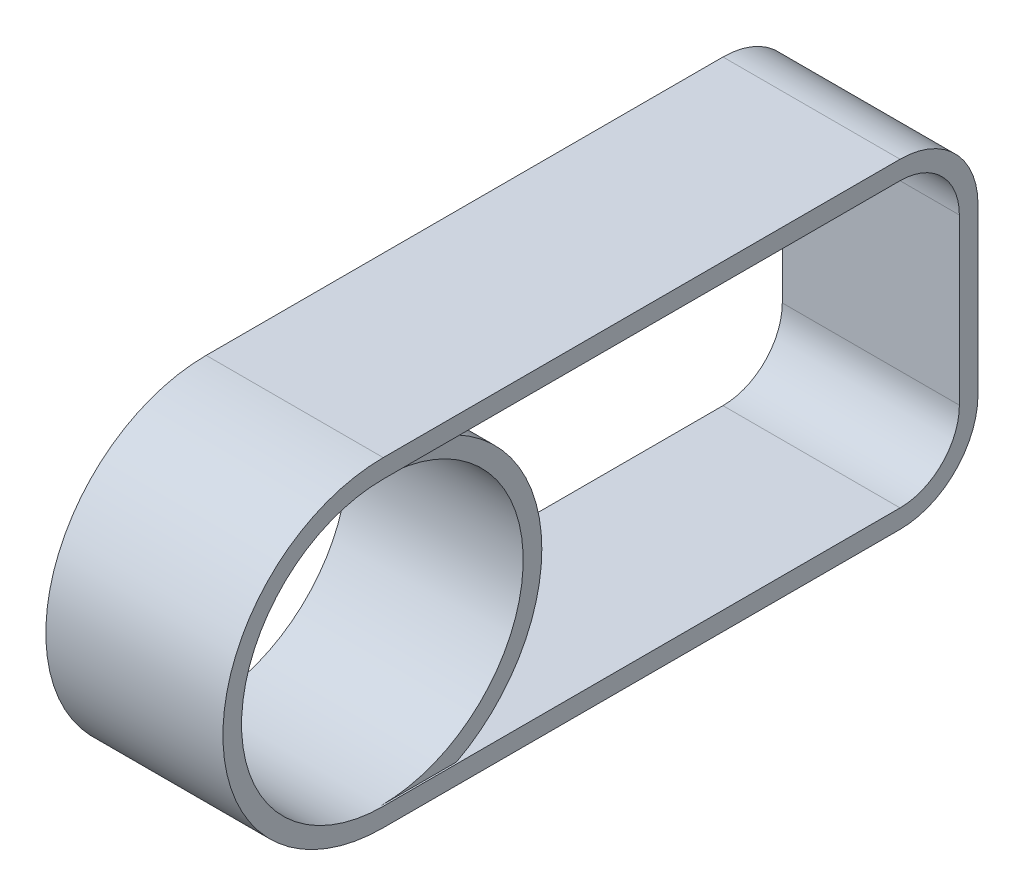
SolidWorks part; units mm, degrees
ref_plane "Front Plane" through (0, 0, 0) normal (0, 0, 1) x (1, 0, 0)
ref_plane "Top Plane" through (0, 0, 0) normal (0, 1, 0) x (1, 0, 0)
ref_plane "Right Plane" through (0, 0, 0) normal (1, 0, 0) x (0, 0, -1)
sketch "Sketch1" plane through (0, 0, 0) normal (1, 0, 0) x (0, 0, -1)
  line L0 (442.7415, 0) -> (3050, 0)
  line L1 (3400, 350) -> (3400, 1322)
  line L2 (3050, 1672) -> (442.7415, 1672)
  line L5 (0, -110) -> (3050, -110)
  line L6 (3510, 350) -> (3510, 1322)
  line L7 (3050, 1782) -> (0, 1782)
  arc A0 (3050, 0) -> (3400, 350) centre (3050, 350) ccw
  arc A1 (3400, 1322) -> (3050, 1672) centre (3050, 1322) ccw
  circle A2 centre (0, 836) radius 836
  arc A3 (3050, -110) -> (3510, 350) centre (3050, 350) ccw
  arc A4 (3510, 1322) -> (3050, 1782) centre (3050, 1322) ccw
  arc A5 (442.7415, 0) -> (442.7415, 1672) centre (0, 836) ccw
  arc A6 (0, 1782) -> (0, -110) centre (0, 836) ccw
  dimension "D2" = 972
  dimension "D1" = 3050
extrude "Boss-Extrude1" add sketch "Sketch1" along normal blind 1045
sketch "Sketch2" plane through (1045, 0, 0) normal (1, 0, 0) x (0, 0, -1)
  line L0 (0, 1672) -> (1071.4939, 1672)
  line L1 (3050, 1672) -> (442.7415, 1672) construction
  line L2 (1071.4939, 1672) -> (1071.4939, 0)
  line L3 (442.7415, 0) -> (3050, 0) construction
  line L4 (1071.4939, 0) -> (0, 0)
  line L5 (0, 0) -> (0, 1672)
  circle A0 centre (0, 836) radius 836 construction
extrude "Cut-Extrude1" cut sketch "Sketch2" against normal blind 10
